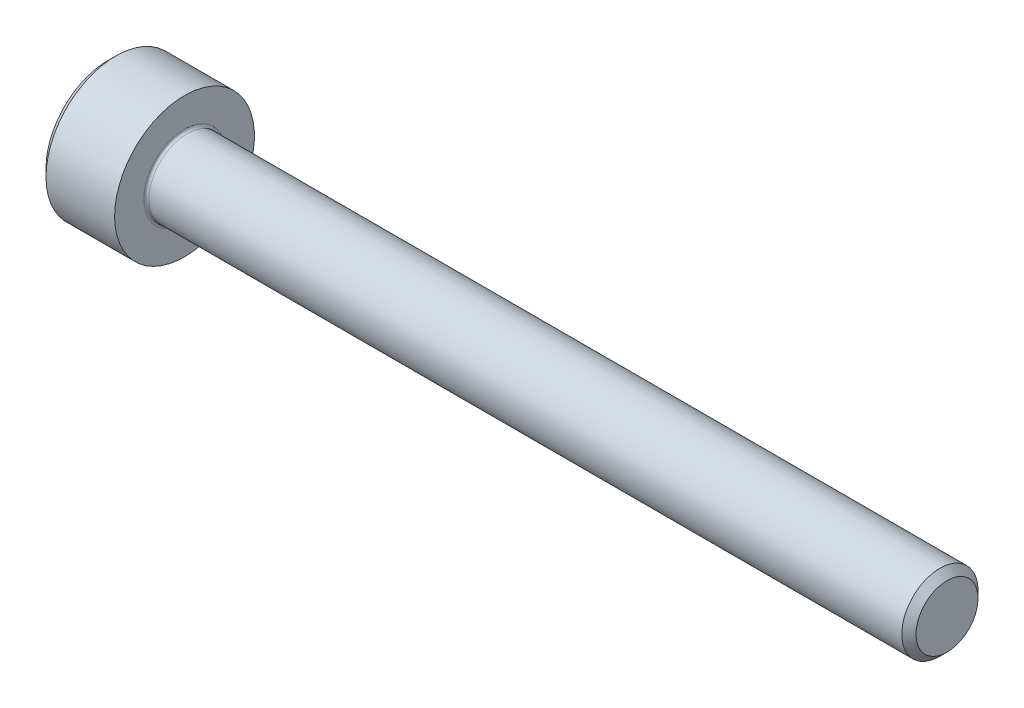
SolidWorks part; units mm, degrees
revolve "Base-Revolve" add sketch "BodySke"
sketch "BodySke" plane through (0, 0, 0) normal (0, 0, 1) x (1, 0, 0)
  line L0 (0, 0) -> (0, 2.45)
  line L1 (0.3, 2.75) -> (3, 2.75)
  line L2 (3, 2.75) -> (3, 1.5)
  line L3 (3, 1.5) -> (32.7195, 1.5)
  line L4 (33, 1.2195) -> (33, 0)
  line L5 (33, 0) -> (0, 0)
  line L6 (-31.75, 0) -> (127, 0) construction
  line L7 (0, 2.45) -> (0.3, 2.75)
  line L8 (33, 1.2195) -> (32.7195, 1.5)
  line L9 (0, -2.45) -> (0.3, -2.75) construction
  line L10 (33, -1.2195) -> (32.7195, -1.5) construction
  line L11 (3.5, 9.525) -> (3.5, 3.175) construction
  line L12 (3, 9.525) -> (3, 3.175) construction
  line L13 (-17, 9.525) -> (-17, 3.175) construction
  dimension "Diameter" = 3
  dimension "Head_ht" = 3
  dimension "Length" = 30
  dimension "Body_ch_ang" = 45
  dimension "Head_dia" = 5.5
  dimension "Head_ch_ang" = 45
  dimension "Minor_dia" = 2.439
  dimension "Advance" = 0.5
  dimension "Thread_nom" = 30
  dimension "Thread_length" = 50
  dimension "Head_ch_ht" = 0.3
cosmetic thread "ThreadCosmetic" [suppressed]
fillet "Fillet1" radius 0.1 1 edges at (3, 0, 1.5)
material "Plain Carbon Steel"
ref_plane "Plane1" through (0, 0, 0) normal (0, 0, 1) x (1, 0, 0)
ref_plane "Plane2" through (0, 0, 0) normal (0, 1, 0) x (1, 0, 0)
ref_plane "Plane3" through (0, 0, 0) normal (1, 0, 0) x (0, 0, -1)
sketch "Sketch2" plane through (0, 0, 0) normal (0, 0, 1) x (1, 0, 0)
  line L0 (0, 1.28) -> (1.3, 1.28)
  line L1 (1.3, 1.28) -> (2.039, 0)
  line L2 (-31.75, 0) -> (127, 0) construction
  line L3 (2.039, 0) -> (0, 0)
  line L4 (0, 0) -> (0, 1.28)
  line L5 (0, 2.45) -> (0, -2.45) construction
  line L6 (0, 0) -> (47.625, 0) construction
  line L7 (3, -2.75) -> (3, 2.75) construction
  dimension "D1" = 1.28
  dimension "D2" = 60
revolve "Hex-PreBroach" cut sketch "Sketch2" angle 360 about L6
sketch "Sketch3" plane through (0, 0, 0) normal (-1, 0, 0) x (0, 0.5, 0.866)
  line L0 (0.739, 1.28) -> (-0.739, 1.28)
  line L1 (-0.739, 1.28) -> (-1.478, 0)
  line L2 (0.739, 1.28) -> (1.478, 0)
  line L3 (0.739, -1.28) -> (1.478, 0)
  line L4 (0.739, -1.28) -> (-0.739, -1.28)
  line L5 (-0.739, -1.28) -> (-1.478, 0)
  dimension "D1" = 1.28
  dimension "D2" = 1.28
  dimension "Hex_size" = 2.56
extrude "Hex" cut sketch "Sketch3" against normal blind 1.3
sketch "Sketch4" plane through (0, 0, 0) normal (-1, 0, 0) x (0, 0, 1)
  line L0 (0, 0) -> (1.4605, 0)
  line L1 (0, 0) -> (6.1484, 3.5498) construction
  line L2 (0, 0) -> (0.7302, 1.2648)
  line L3 (1.2009, 0.3267) -> (1.3933, 0.4378)
  line L4 (0.8834, 0.8767) -> (1.0758, 0.9877)
  arc A0 (1.2009, 0.3267) -> (0.8834, 0.8767) centre (0, 0) ccw
  arc A1 (1.4605, 0) -> (1.3933, 0.4378) centre (0, 0) ccw
  arc A2 (0.7302, 1.2648) -> (1.0758, 0.9877) centre (0, 0) cw
  dimension "D1" = 30
  dimension "D2" = 60
  dimension "Spline_p_dim" = 0.635
  dimension "D3" = 0.3175
extrude "Spline" [suppressed] cut sketch "Sketch4" against normal blind 1.3
pattern_circular "CirPattern1" [suppressed] count 6 every 60
sketch "Sketch5" plane through (0, 0, 0) normal (0, 0, 1) x (1, 0, 0)
  line L0 (-31.75, 0) -> (127, 0) construction
  line L2 (0, 2.45) -> (0, -2.45) construction
  circle A0 centre (1.2, 0) radius 0.475
  dimension "Drilled_hole_dia" = 0.95
  dimension "Drilled_hole_loc" = 1.2
extrude "Hole" [suppressed] cut sketch "Sketch5" against normal through all and the other way through all
pattern_circular "Drilled-4" [suppressed] count 2 every 60
pattern_circular "Drilled-6" [suppressed] count 3 every 60
sketch "ThdSchSke" plane through (0, 0, 0) normal (0, 0, 1) x (1, 0, 0)
  line L0 (3.5, -1.2195) -> (3.3036, -1.5)
  line L1 (3.5, -1.2195) -> (3.6964, -1.5)
  line L2 (3.6964, -1.5) -> (3.6964, -1.875)
  line L3 (-3.175, 0) -> (5.1513, 0) construction
  line L5 (3.6964, -1.875) -> (3.3036, -1.875)
  line L6 (3.3036, -1.875) -> (3.3036, -1.5)
  line L7 (0, 2.45) -> (0, -2.45) construction
  dimension "Thread_minor" = 2.439
  dimension "Diameter" = 3
  dimension "Start" = 3.5
revolve "ThreadSchematic" [suppressed] cut sketch "ThdSchSke" angle 360 about L3
pattern_linear "ThdSchPat" [suppressed]
equation "\"D2@Sketch3\" = \"Hex_size@Sketch3\" / 2"
equation "\"D1@Sketch3\" = \"Hex_size@Sketch3\" / 2"
equation "\"D1@Sketch2\" = \"Hex_size@Sketch3\" / 2"
equation "\"D3@Sketch4\" = \"Spline_p_dim@Sketch4\" / 2"
equation "\"Thread_minor@ThreadCosmetic\"  =  \"Minor_dia@BodySke\""
equation "\"D2@CirPattern1\" = 360 / \"Num_teeth@CirPattern1\""
equation "\"Wall_thickness@Sketch2\" = \"Head_ht@BodySke\" - \"Key_eng@Hex\""
equation "\"Thread_length@ThreadCosmetic\" = ((sgn( (\"Length@BodySke\" - \"Advance@BodySke\" ) - \"Thread_nom@BodySke\" )-1)*( (\"Length@BodySke\" - \"Advance@BodySke\" ) - \"Thread_nom@BodySke\" ))/-2+ \"Thread_nom@BodySke\""
equation "\"Thread_minor@ThdSchSke\" = \"Minor_dia@BodySke\""
equation "\"Diameter@ThdSchSke\" = \"Diameter@BodySke\""
equation "\"Overcut@ThdSchSke\" = \"Diameter@BodySke\" * 1.25"
equation "\"Start@ThdSchSke\" = \"Head_ht@BodySke\" + \"Length@BodySke\" - \"Thread_length@ThreadCosmetic\"  '---Non-countersunk---"
equation "\"Num_threads@ThdSchPat\" = int( \"Thread_length@ThreadCosmetic\" / \"Advance@BodySke\" + 0.999 )  + 1"
equation "\"Advance@ThdSchPat\" = \"Thread_length@ThreadCosmetic\" /  (\"Num_threads@ThdSchPat\" - 1) 'relax it"
equation "\"Num_threads@ThdSchPat\" = \"Num_threads@ThdSchPat\" - sgn( \"Num_threads@ThdSchPat\" - 1) '---chamfered tips only---"
